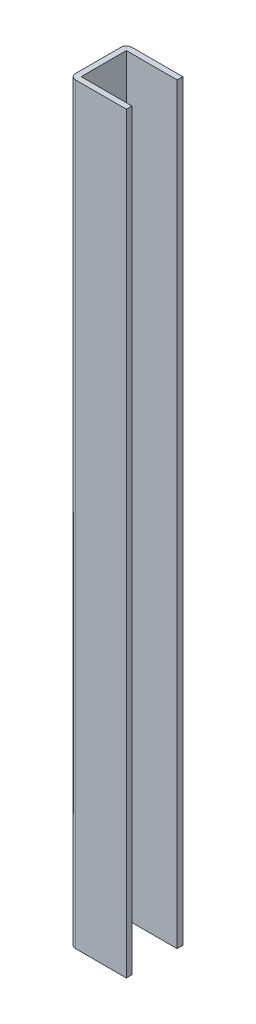
SolidWorks part; units mm, degrees
ref_plane "Спереди" through (0, 0, 0) normal (0, 0, 1) x (1, 0, 0)
ref_plane "Сверху" through (0, 0, 0) normal (0, 1, 0) x (1, 0, 0)
ref_plane "Справа" through (0, 0, 0) normal (1, 0, 0) x (0, 0, -1)
sketch "Эскиз1" plane through (0, 0, 0) normal (0, 1, 0) x (1, 0, 0)
  line L1 (-37, 15) -> (37, 15)
  line L2 (-40, 12) -> (-40, -12)
  line L3 (-37, -15) -> (37, -15)
  line L4 (40, 12) -> (40, -12)
  line L5 (-40, 15) -> (40, -15) construction
  line L6 (-40, -15) -> (40, 15) construction
  arc A0 (-37, 15) -> (-40, 12) centre (-37, 12) ccw
  arc A1 (-40, -12) -> (-37, -15) centre (-37, -12) ccw
  arc A2 (37, -15) -> (40, -12) centre (37, -12) ccw
  arc A3 (37, 15) -> (40, 12) centre (37, 12) cw
  point P0 (0, 0)
  dimension "D1" = 3
extrude "Вытянуть-Тонкостенный1" add sketch "Эскиз1" along normal blind 400 thin
sketch "Эскиз2" plane through (0, 400, 0) normal (0, 1, 0) x (1, 0, 0)
  line L1 (-10, -23.0623) -> (41.1465, -23.0623)
  line L2 (-10, -23.0623) -> (-10, 20.9728)
  line L3 (-10, 20.9728) -> (41.1465, 20.9728)
  line L4 (41.1465, -23.0623) -> (41.1465, 20.9728)
extrude "Вырез-Вытянуть1" cut sketch "Эскиз2" against normal through all
